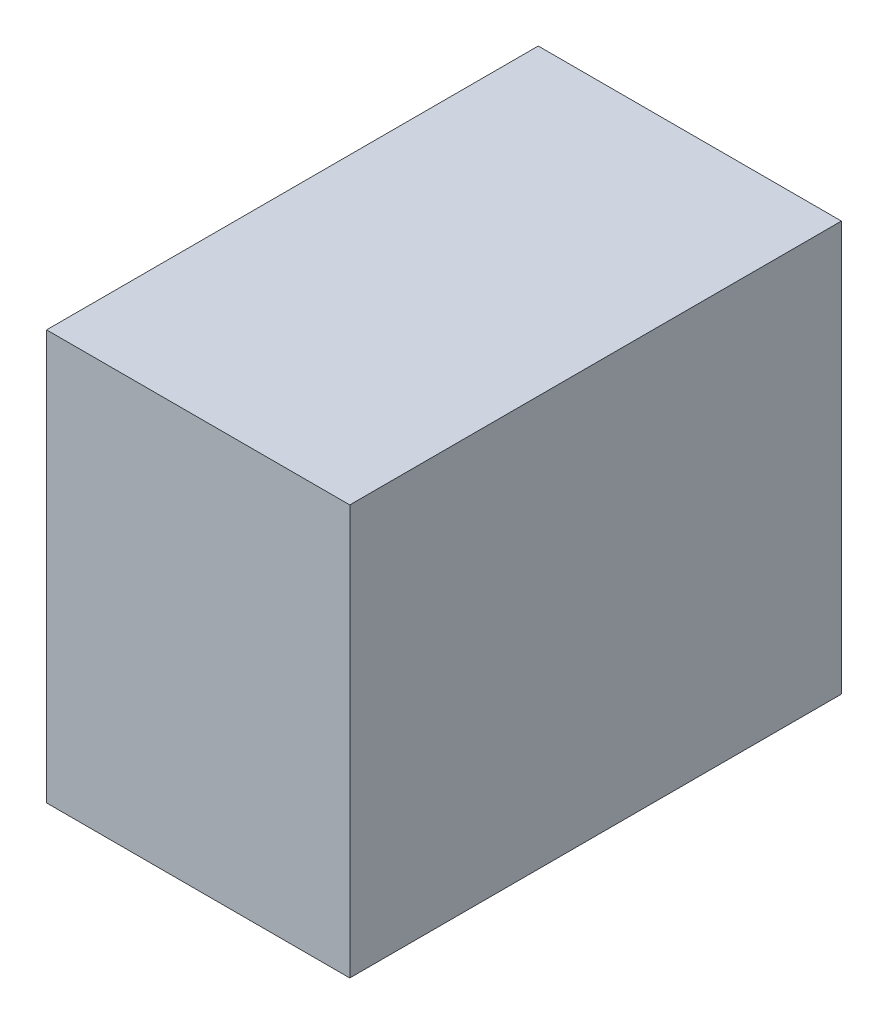
SolidWorks part; units mm, degrees
ref_plane "Front Plane" through (0, 0, 0) normal (0, 0, 1) x (1, 0, 0)
ref_plane "Top Plane" through (0, 0, 0) normal (0, 1, 0) x (1, 0, 0)
ref_plane "Right Plane" through (0, 0, 0) normal (1, 0, 0) x (0, 0, -1)
sketch "Sketch1" plane through (0, 0, 0) normal (0, 1, 0) x (1, 0, 0)
  line L1 (-469.9, -762) -> (469.9, -762)
  line L2 (-469.9, -762) -> (-469.9, 762)
  line L3 (-469.9, 762) -> (469.9, 762)
  line L4 (469.9, -762) -> (469.9, 762)
  line L5 (-469.9, -762) -> (469.9, 762) construction
  line L6 (-469.9, 762) -> (469.9, -762) construction
  point P0 (0, 0)
  dimension "D1" = 939.8
  dimension "D2" = 1524
extrude "Boss-Extrude1" add sketch "Sketch1" along normal mid plane 1270
